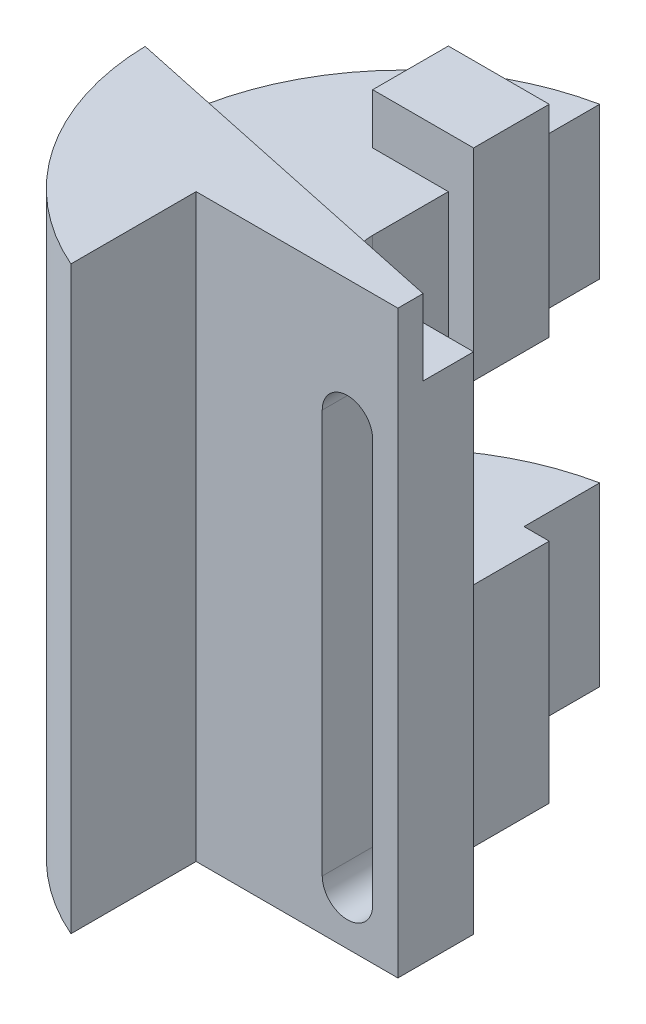
SolidWorks part; units mm, degrees
material "1060 Alloy"
ref_plane "Front Plane" through (0, 0, 0) normal (0, 0, 1) x (1, 0, 0)
ref_plane "Top Plane" through (0, 0, 0) normal (0, 1, 0) x (1, 0, 0)
ref_plane "Right Plane" through (0, 0, 0) normal (1, 0, 0) x (0, 0, -1)
sketch "Sketch1" plane through (0, 0, 0) normal (0, 1, 0) x (1, 0, 0)
  line L0 (0, 0) -> (0, -15)
  line L1 (0, -15) -> (-40, -15)
  line L2 (-40, -15) -> (-40, -39.8156)
  line L3 (0, 0) -> (-20, 0)
  line L4 (-30, 10) -> (-30, 55)
  arc A0 (-20, 0) -> (-30, 10) centre (-20, 10) cw
  arc A1 (-30, 55) -> (-40, -39.8156) centre (-20, 6.0102) ccw
  point P9 (-30, 0)
  dimension "D5" = 10
  dimension "D6" = 100
  dimension "D1" = 15
  dimension "D2" = 40
  dimension "D3" = 55
  dimension "D4" = 30
  dimension "D7" = 20
extrude "Boss-Extrude1" add sketch "Sketch1" along normal blind 115
sketch "Sketch2" plane through (-30, 0, 0) normal (1, 0, 0) x (0, 0, -1)
  line L0 (55, 115) -> (55, 0) construction
  line L1 (55, 70) -> (15, 70)
  line L2 (55, 70) -> (55, 35)
  line L3 (55, 35) -> (15, 35)
  line L4 (15, 70) -> (15, 35)
  line L6 (10, 115) -> (55, 115) construction
  dimension "D1" = 35
  dimension "D2" = 45
  dimension "D3" = 40
extrude "Cut-Extrude1" cut sketch "Sketch2" against normal through all
sketch "Sketch3" plane through (0, 0, 0) normal (0, 0, -1) x (-1, 0, 0)
  line L0 (0, 0) -> (20, 0) construction
  line L1 (0, 115) -> (0, 0) construction
  line L4 (15, 90) -> (15, 10)
  line L6 (5, 90) -> (5, 10)
  arc A0 (5, 10) -> (15, 10) centre (10, 10) ccw
  arc A2 (5, 90) -> (15, 90) centre (10, 90) cw
  dimension "D1" = 5
  dimension "D4" = 80
  dimension "D2" = 10
  dimension "D3" = 10
extrude "Cut-Extrude2" cut sketch "Sketch3" against normal up to next
sketch "Sketch4" plane through (-30, 0, 0) normal (1, 0, 0) x (0, 0, -1)
  line L0 (15, 35) -> (55, 35) construction
  line L1 (40, 35) -> (25, 35)
  line L2 (40, 35) -> (40, -10)
  line L3 (40, -10) -> (25, -10)
  line L4 (25, 35) -> (25, -10)
  line L5 (55, 70) -> (15, 70) construction
  line L6 (40, 70) -> (25, 70)
  line L7 (40, 70) -> (40, 110)
  line L8 (40, 110) -> (25, 110)
  line L9 (25, 70) -> (25, 110)
  line L10 (10, 0) -> (55, 0) construction
  line L11 (15, 70) -> (15, 35) construction
  line L13 (55, 115) -> (55, 70) construction
  dimension "D1" = 15
  dimension "D2" = 10
  dimension "D3" = 10
  dimension "D4" = 40
  dimension "D5" = 15
  dimension "D6" = 15
extrude "Boss-Extrude2" add sketch "Sketch4" along normal blind 5
sketch "Sketch6" plane through (0, 115, 0) normal (0, 1, 0) x (1, 0, 0)
  line L0 (0, -10) -> (-69.9871, 4.8762)
  line L1 (0, -15) -> (0, 0) construction
  line L2 (-40, -15) -> (0, -15) construction
  line L3 (0, -10) -> (0, 0)
  line L4 (0, 0) -> (-20, 0)
  line L5 (-30, 55) -> (-30, 10)
  arc A0 (-30, 55) -> (-69.9871, 4.8762) centre (-20, 6.0102) ccw
  arc A1 (-30, 10) -> (-20, 0) centre (-20, 10) ccw
  dimension "D2" = 5
  dimension "D3" = 78
extrude "Cut-Extrude3" cut sketch "Sketch6" against normal blind 15
sketch "Sketch7" plane through (0, 100, 0) normal (0, 1, 0) x (1, 0, 0)
  line L1 (-30, 40) -> (-45, 40)
  line L2 (-30, 40) -> (-30, 25)
  line L3 (-30, 25) -> (-45, 25)
  line L4 (-45, 40) -> (-45, 25)
  dimension "D1" = 15
  dimension "D2" = 15
extrude "Boss-Extrude3" add sketch "Sketch7" along normal blind 10
sketch "Sketch8" plane through (0, 0, 0) normal (0, -1, 0) x (1, 0, 0)
  line L1 (-30, -25) -> (-45.0025, -25)
  line L2 (-30, -25) -> (-30, -40)
  line L3 (-30, -40) -> (-45.0025, -40)
  line L4 (-45.0025, -25) -> (-45.0025, -40)
  dimension "D1" = 15
  dimension "D2" = 15.0025
extrude "Boss-Extrude4" add sketch "Sketch8" along normal blind 10
equation "\"A\" = 50"
equation "\"B\" = 55"
equation "\"C\" = 35"
